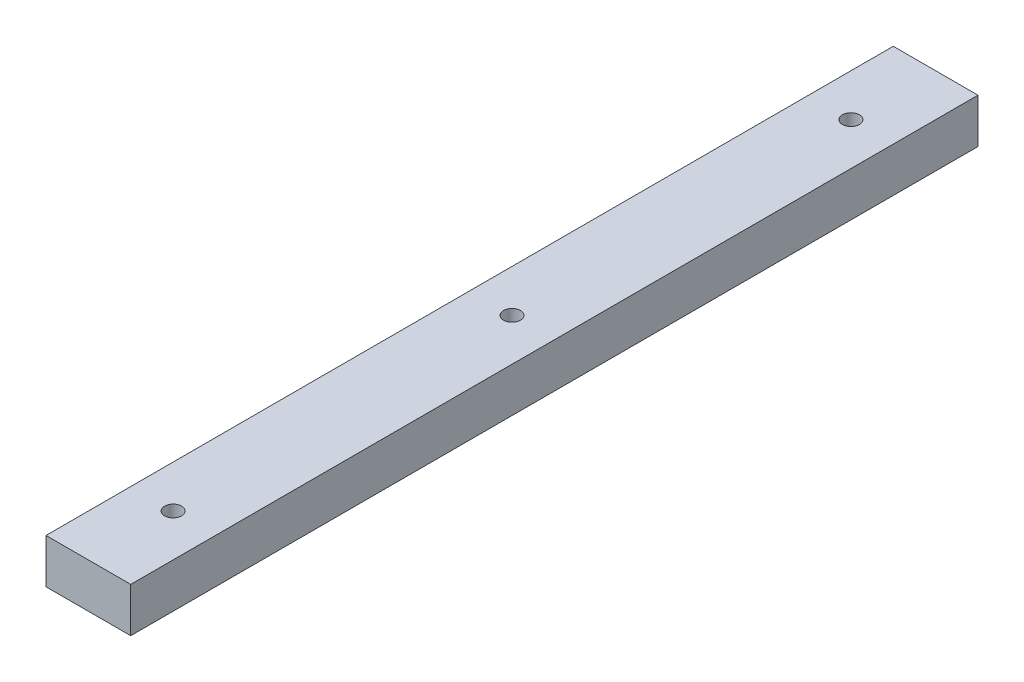
SolidWorks part; units mm, degrees
ref_plane "Front Plane" through (0, 0, 0) normal (0, 0, 1) x (1, 0, 0)
ref_plane "Top Plane" through (0, 0, 0) normal (0, 1, 0) x (1, 0, 0)
ref_plane "Right Plane" through (0, 0, 0) normal (1, 0, 0) x (0, 0, -1)
sketch "Sketch1" plane through (0, 0, 0) normal (0, 1, 0) x (1, 0, 0)
  line L0 (0, 100) -> (0, -100) construction
  line L1 (-10, -100) -> (10, -100)
  line L2 (-10, -100) -> (-10, 100)
  line L3 (-10, 100) -> (10, 100)
  line L4 (10, -100) -> (10, 100)
  line L5 (-10, -100) -> (10, 100) construction
  line L6 (-10, 100) -> (10, -100) construction
  circle A0 centre (0, 80) radius 2
  circle A1 centre (0, 0) radius 2
  circle A2 centre (0, -80) radius 2
  point P0 (0, 0)
  dimension "D3" = 4
  dimension "D4" = 20
  dimension "D5" = 20
  dimension "D1" = 200
  dimension "D2" = 20
extrude "Boss-Extrude1" add sketch "Sketch1" along normal blind 10.5
